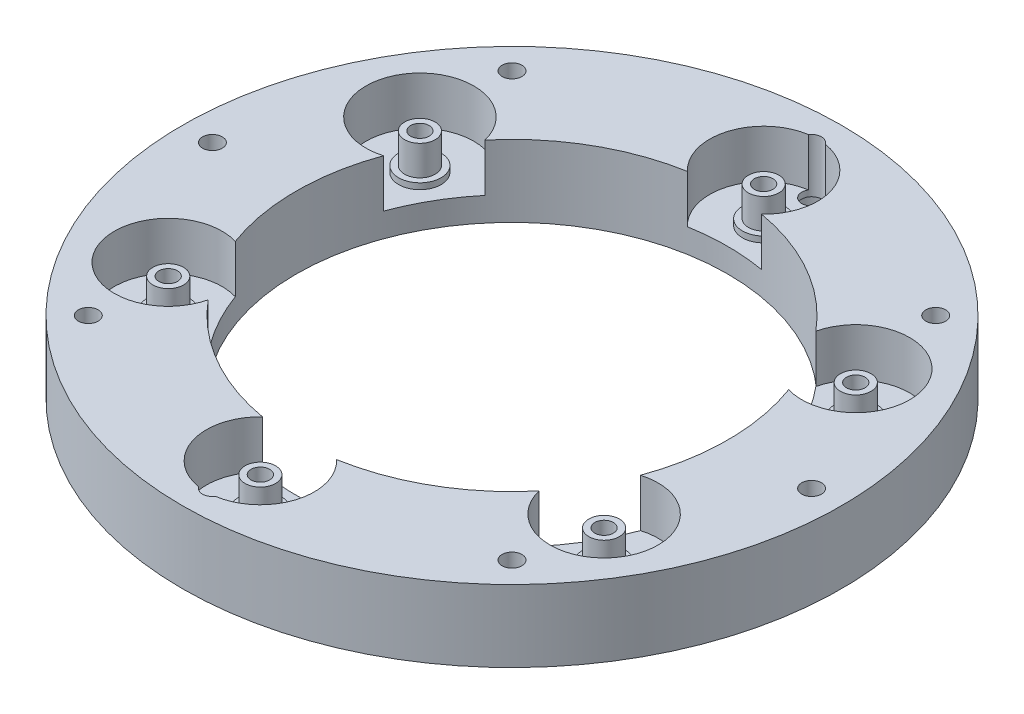
SolidWorks part; units mm, degrees
ref_plane "Front Plane" through (0, 0, 0) normal (0, 0, 1) x (1, 0, 0)
ref_plane "Top Plane" through (0, 0, 0) normal (0, 1, 0) x (1, 0, 0)
ref_plane "Right Plane" through (0, 0, 0) normal (1, 0, 0) x (0, 0, -1)
sketch "Sketch1" plane through (0, 0, 0) normal (0, 1, 0) x (1, 0, 0)
  circle A0 centre (0, 0) radius 36
  circle A1 centre (0, 0) radius 55
  circle A2 centre (0, 42) radius 1.55
  circle A3 centre (36.3731, 21) radius 1.55
  circle A4 centre (36.3731, -21) radius 1.55
  circle A5 centre (0, -42) radius 1.55
  circle A6 centre (-36.3731, -21) radius 1.55
  circle A7 centre (-36.3731, 21) radius 1.55
  point P18 (0, 0)
  dimension "D1" = 72
  dimension "D2" = 110
  dimension "D4" = 3.1
  dimension "D3" = 42
  dimension "D5" = 6
extrude "Boss-Extrude1" add sketch "Sketch1" along normal blind 4
sketch "Sketch3" plane through (0, 4, 0) normal (0, 1, 0) x (1, 0, 0)
  circle A0 centre (-36.3731, 21) radius 3.55
  circle A1 centre (-36.3731, 21) radius 1.55
  circle A2 centre (-36.3731, 21) radius 1.55
  circle A3 centre (0, -42) radius 1.55
  circle A4 centre (0, -42) radius 1.55
  circle A5 centre (36.3731, 21) radius 1.55
  circle A6 centre (36.3731, 21) radius 1.55
  circle A7 centre (0, 42) radius 1.55
  circle A8 centre (0, 42) radius 1.55
  circle A9 centre (36.3731, -21) radius 1.55
  circle A10 centre (36.3731, -21) radius 1.55
  circle A11 centre (-36.3731, -21) radius 1.55
  circle A12 centre (-36.3731, -21) radius 1.55
  circle A13 centre (0, -42) radius 3.55
  circle A14 centre (36.3731, 21) radius 3.55
  circle A15 centre (0, 42) radius 3.55
  circle A16 centre (36.3731, -21) radius 3.55
  circle A17 centre (-36.3731, -21) radius 3.55
  dimension "D1" = 0
  dimension "D2" = 0
  dimension "D3" = 0
  dimension "D4" = 0
  dimension "D5" = 0
  dimension "D6" = 0
  dimension "D7" = 2
extrude "Boss-Extrude2" add sketch "Sketch3" along normal blind 1
sketch "Sketch5" plane through (0, 5, 0) normal (0, 1, 0) x (1, 0, 0)
  circle A0 centre (-36.3731, -21) radius 2.55
  circle A1 centre (-36.3731, -21) radius 1.55
  circle A2 centre (-36.3731, -21) radius 1.55
  circle A3 centre (0, -42) radius 1.55
  circle A4 centre (0, -42) radius 1.55
  circle A5 centre (36.3731, -21) radius 1.55
  circle A6 centre (36.3731, -21) radius 1.55
  circle A7 centre (36.3731, 21) radius 1.55
  circle A8 centre (36.3731, 21) radius 1.55
  circle A9 centre (0, 42) radius 1.55
  circle A10 centre (0, 42) radius 1.55
  circle A11 centre (-36.3731, 21) radius 1.55
  circle A12 centre (-36.3731, 21) radius 1.55
  circle A13 centre (0, -42) radius 2.55
  circle A14 centre (36.3731, -21) radius 2.55
  circle A15 centre (36.3731, 21) radius 2.55
  circle A16 centre (0, 42) radius 2.55
  circle A17 centre (-36.3731, 21) radius 2.55
  dimension "D1" = 0
  dimension "D2" = 0
  dimension "D3" = 0
  dimension "D4" = 0
  dimension "D5" = 0
  dimension "D6" = 0
  dimension "D7" = 1
extrude "Boss-Extrude3" add sketch "Sketch5" along normal blind 5
sketch "Sketch6" plane through (0, 4, 0) normal (0, 1, 0) x (1, 0, 0)
  circle A2 centre (0, 0) radius 55
  arc A3 (6.1874, 35.4643) -> (-6.1874, 35.4643) centre (0, 42) ccw
  arc A4 (33.8067, 12.3737) -> (27.6193, 23.0906) centre (36.3731, 21) ccw
  arc A5 (27.6193, -23.0906) -> (33.8067, -12.3737) centre (36.3731, -21) ccw
  arc A6 (-6.1874, -35.4643) -> (6.1874, -35.4643) centre (0, -42) ccw
  arc A7 (-33.8067, -12.3737) -> (-27.6193, -23.0906) centre (-36.3731, -21) ccw
  arc A8 (-27.6193, 23.0906) -> (-33.8067, 12.3737) centre (-36.3731, 21) ccw
  circle A9 centre (0, 0) radius 36 construction
  arc A10 (-33.8067, 12.3737) -> (-33.8067, -12.3737) centre (0, 0) ccw
  arc A11 (-6.1874, 35.4643) -> (-27.6193, 23.0906) centre (0, 0) ccw
  arc A12 (27.6193, 23.0906) -> (6.1874, 35.4643) centre (0, 0) ccw
  arc A13 (33.8067, -12.3737) -> (33.8067, 12.3737) centre (0, 0) ccw
  arc A14 (6.1874, -35.4643) -> (27.6193, -23.0906) centre (0, 0) ccw
  arc A15 (-27.6193, -23.0906) -> (-6.1874, -35.4643) centre (0, 0) ccw
  point P20 (0, 0)
  dimension "D1" = 18
  dimension "D3" = 110
  dimension "D4" = 6
extrude "Boss-Extrude4" add sketch "Sketch6" along normal blind 8
sketch "Sketch8" plane through (0, 12, 0) normal (0, 1, 0) x (1, 0, 0)
  circle A0 centre (0, 50) radius 1.65
  circle A1 centre (35.3553, 35.3553) radius 1.65
  circle A2 centre (50, 0) radius 1.65
  circle A3 centre (35.3553, -35.3553) radius 1.65
  circle A4 centre (0, -50) radius 1.65
  circle A5 centre (-35.3553, -35.3553) radius 1.65
  circle A6 centre (-50, 0) radius 1.65
  circle A7 centre (-35.3553, 35.3553) radius 1.65
  point P20 (0, 0)
  dimension "D1" = 3.3
  dimension "D2" = 50
  dimension "D3" = 8
extrude "Cut-Extrude2" cut sketch "Sketch8" against normal through all
sketch "Sketch7" plane through (0, 0, 0) normal (0, -1, 0) x (1, 0, 0)
  circle A1 centre (-36.3731, -21) radius 3.55
  circle A3 centre (-36.3731, -21) radius 1.55
  circle A5 centre (-36.3731, -21) radius 1.55
  circle A7 centre (-36.3731, 21) radius 1.55
  circle A9 centre (-36.3731, 21) radius 1.55
  circle A11 centre (0, 42) radius 1.55
  circle A18 centre (0, 42) radius 1.55
  circle A19 centre (36.3731, 21) radius 1.55
  circle A20 centre (36.3731, 21) radius 1.55
  circle A21 centre (36.3731, -21) radius 1.55
  circle A22 centre (36.3731, -21) radius 1.55
  circle A23 centre (0, -42) radius 1.55
  circle A24 centre (0, -42) radius 1.55
  circle A25 centre (-35.3553, -35.3553) radius 1.65
  circle A26 centre (-35.3553, -35.3553) radius 1.65
  circle A27 centre (-50, 0) radius 1.65
  circle A28 centre (-50, 0) radius 1.65
  circle A29 centre (-35.3553, 35.3553) radius 1.65
  circle A30 centre (-35.3553, 35.3553) radius 1.65
  circle A31 centre (0, 50) radius 1.65
  circle A32 centre (0, 50) radius 1.65
  circle A33 centre (35.3553, 35.3553) radius 1.65
  circle A34 centre (35.3553, 35.3553) radius 1.65
  circle A35 centre (50, 0) radius 1.65
  circle A36 centre (50, 0) radius 1.65
  circle A37 centre (35.3553, -35.3553) radius 1.65
  circle A38 centre (35.3553, -35.3553) radius 1.65
  circle A39 centre (0, -50) radius 1.65
  circle A40 centre (0, -50) radius 1.65
  circle A41 centre (-36.3731, 21) radius 3.55
  circle A42 centre (0, 42) radius 3.55
  circle A43 centre (36.3731, 21) radius 3.55
  circle A44 centre (36.3731, -21) radius 3.55
  circle A45 centre (0, -42) radius 3.55
  circle A46 centre (-35.3553, -35.3553) radius 3.65
  circle A47 centre (-50, 0) radius 3.65
  circle A48 centre (-35.3553, 35.3553) radius 3.65
  circle A49 centre (0, 50) radius 3.65
  circle A50 centre (35.3553, 35.3553) radius 3.65
  circle A51 centre (50, 0) radius 3.65
  circle A52 centre (35.3553, -35.3553) radius 3.65
  circle A53 centre (0, -50) radius 3.65
  dimension "D1" = 0
  dimension "D2" = 0
  dimension "D3" = 0
  dimension "D4" = 0
  dimension "D5" = 0
  dimension "D6" = 0
  dimension "D7" = 0
  dimension "D8" = 0
  dimension "D9" = 0
  dimension "D10" = 0
  dimension "D11" = 0
  dimension "D12" = 0
  dimension "D13" = 0
  dimension "D14" = 0
  dimension "D15" = 2
extrude "Cut-Extrude1" cut sketch "Sketch7" against normal blind 3
